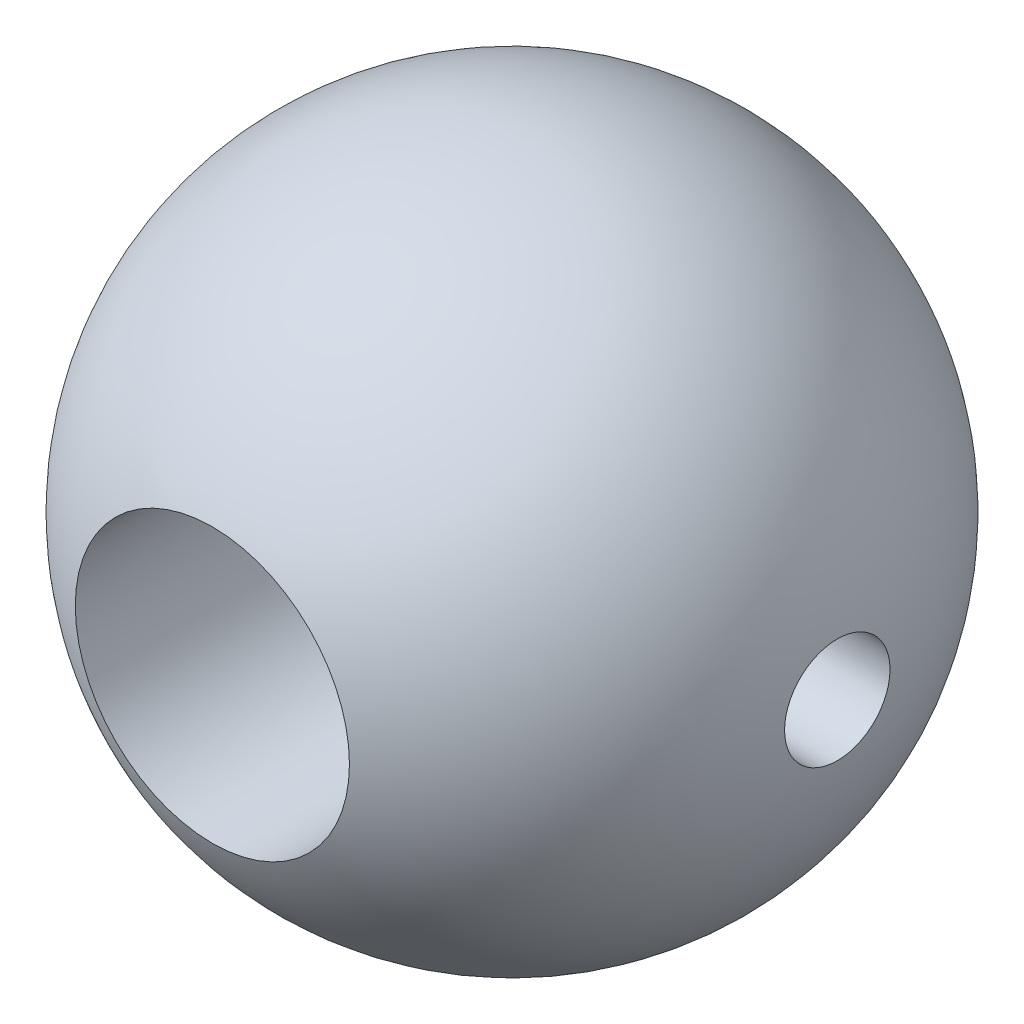
SolidWorks part; units mm, degrees
ref_plane "Front Plane" through (0, 0, 0) normal (0, 0, 1) x (1, 0, 0)
ref_plane "Top Plane" through (0, 0, 0) normal (0, 1, 0) x (1, 0, 0)
ref_plane "Right Plane" through (0, 0, 0) normal (1, 0, 0) x (0, 0, -1)
sketch "Sketch1" plane through (0, 0, 0) normal (0, 1, 0) x (1, 0, 0)
  line L0 (0, -16.1722) -> (0, 21.6944) construction
  line L1 (3.9624, 8.6617) -> (3.9624, -8.6617)
  arc A0 (3.9624, -8.6617) -> (3.9624, 8.6617) centre (0, 0) ccw
  dimension "D1" = 9.525
  dimension "D2" = 3.9624
revolve "Revolve1" add sketch "Sketch1" angle 360 about L0
sketch "Sketch2" plane through (0, 0, 0) normal (0, 1, 0) x (1, 0, 0)
  line L1 (14.1131, 0) -> (-17.2414, 0)
  line L2 (14.1131, 0) -> (14.1131, 1.524)
  line L3 (14.1131, 1.524) -> (-17.2414, 1.524)
  line L4 (-17.2414, 0) -> (-17.2414, 1.524)
  dimension "D1" = 1.524
revolve "Cut-Revolve1" cut sketch "Sketch2" angle 360 about L1
